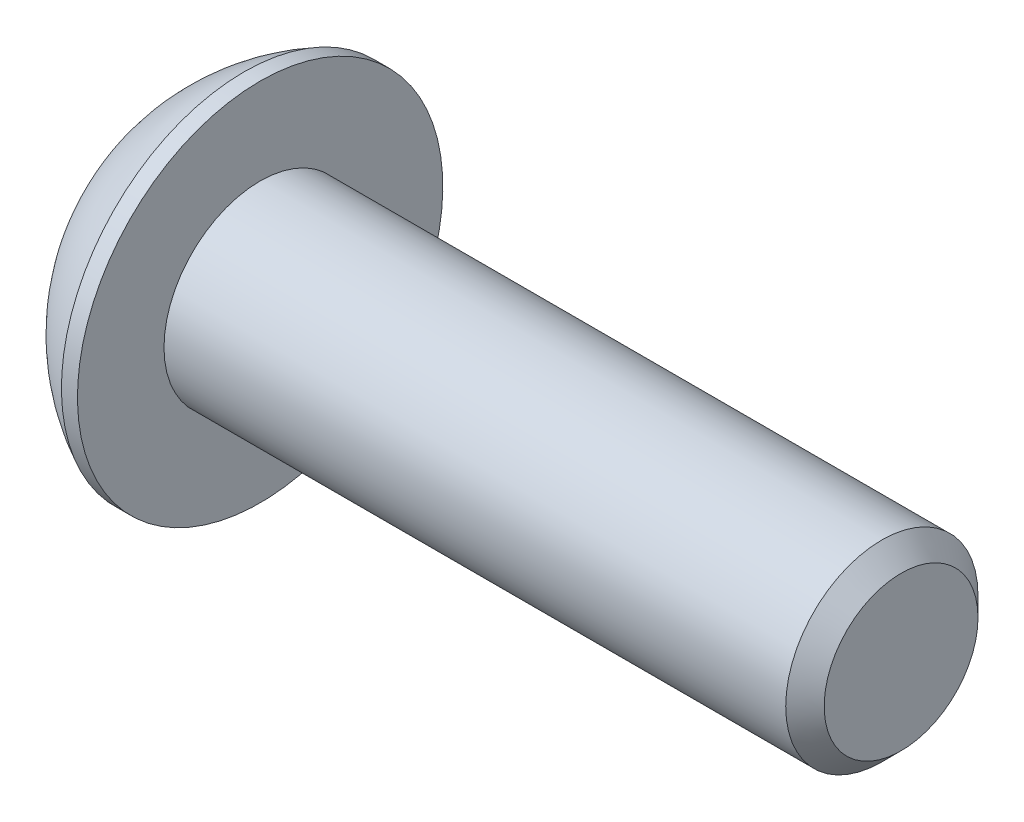
SolidWorks part; units mm, degrees
material "Plain Carbon Steel"
ref_plane "Front Plane" through (0, 0, 0) normal (0, 0, 1) x (1, 0, 0)
ref_plane "Top Plane" through (0, 0, 0) normal (0, 1, 0) x (1, 0, 0)
ref_plane "Right Plane" through (0, 0, 0) normal (1, 0, 0) x (0, 0, -1)
sketch "Sketch2" plane through (0, 0, 0) normal (1, 0, 0) x (0, 0, -1)
  circle A0 centre (0, 0) radius 1.5
  dimension "D1" = 3
extrude "Boss-Extrude1" add sketch "Sketch2" against normal blind 10
chamfer "Chamfer1" distance 0.3 angle 45 1 edges at (0, 0, -1.5)
sketch "Sketch6" plane through (0, 0, 0) normal (0, 0, 1) x (1, 0, 0)
  line L0 (-11.65, 0) -> (-11.65, 1.5)
  line L1 (-11.65, 0) -> (-10, 0)
  line L2 (-10.25, 2.85) -> (-10, 2.85)
  line L6 (-10, 2.85) -> (-10, 0)
  line L8 (-10, 0) -> (-14.6471, 0) construction
  line L10 (-10, 1.5) -> (-10, -1.5) construction
  arc A0 (-11.65, 1.5) -> (-10.25, 2.85) centre (-8.8527, 0) cw
  dimension "D3" = 0.25
  dimension "D1" = 5.7
  dimension "D2" = 1.65
  dimension "D4" = 3
revolve "Revolve1" add sketch "Sketch6" angle 360 about L8
sketch "Sketch7" plane through (-11.65, 0, 0) normal (-1, 0, 0) x (0, 0, 1)
  line L1 (0, 1.1547) -> (-1, 0.5774)
  line L2 (-1, 0.5774) -> (-1, -0.5774)
  line L3 (-1, -0.5774) -> (0, -1.1547)
  line L4 (0, -1.1547) -> (1, -0.5774)
  line L5 (1, -0.5774) -> (1, 0.5774)
  line L6 (1, 0.5774) -> (0, 1.1547)
  circle A0 centre (0, 0) radius 1 construction
  dimension "D1" = 2
extrude "Cut-Extrude1" cut sketch "Sketch7" against normal blind 1.2
sketch "Sketch8" plane through (-11.65, 0, 0) normal (-1, 0, 0) x (0, 0, 1)
  circle A0 centre (0, 0) radius 1.2047
  dimension "D1" = 0.05
extrude "Cut-Extrude2" cut sketch "Sketch8" against normal blind 1 draft 45
